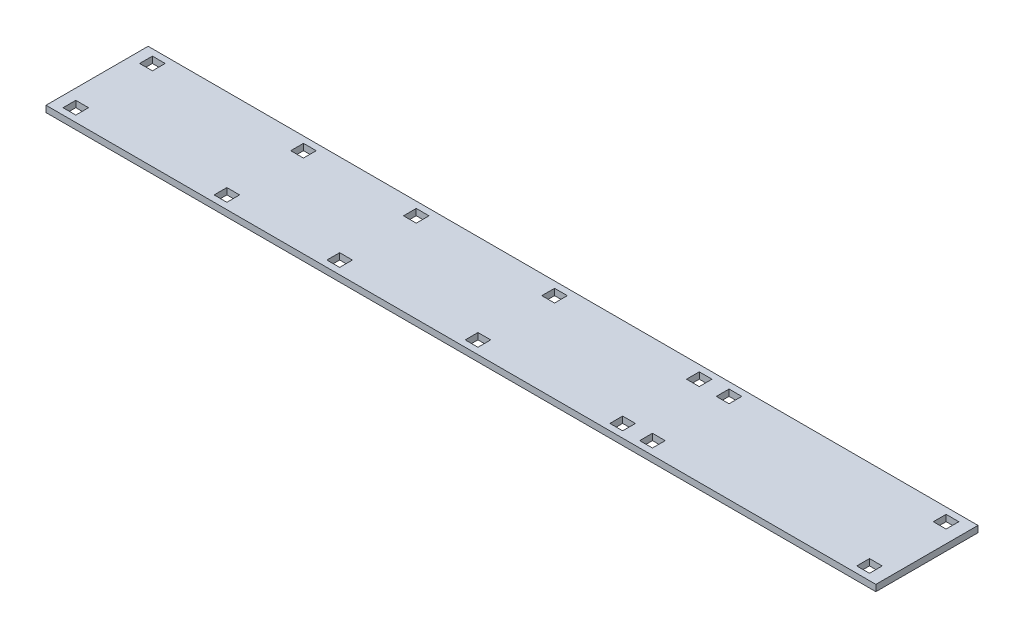
SolidWorks part; units mm, degrees
ref_plane "Front Plane" through (0, 0, 0) normal (0, 0, 1) x (1, 0, 0)
ref_plane "Top Plane" through (0, 0, 0) normal (0, 1, 0) x (1, 0, 0)
ref_plane "Right Plane" through (0, 0, 0) normal (1, 0, 0) x (0, 0, -1)
sketch "Sketch1" plane through (0, 0, 0) normal (0, 1, 0) x (1, 0, 0)
  line L0 (64.5, 4.5) -> (67.5, 4.5)
  line L1 (0, 0) -> (195, 0)
  line L2 (0, 0) -> (0, 24)
  line L3 (0, 24) -> (195, 24)
  line L4 (195, 0) -> (195, 24)
  line L5 (2.5, 22.5) -> (5.5, 22.5)
  line L6 (2.5, 22.5) -> (2.5, 19.5)
  line L7 (2.5, 19.5) -> (5.5, 19.5)
  line L8 (5.5, 22.5) -> (5.5, 19.5)
  line L9 (2.5, 22.5) -> (5.5, 19.5) construction
  line L10 (2.5, 19.5) -> (5.5, 22.5) construction
  line L11 (64.5, 4.5) -> (64.5, 1.5)
  line L12 (64.5, 1.5) -> (67.5, 1.5)
  line L13 (67.5, 4.5) -> (67.5, 1.5)
  line L14 (64.5, 4.5) -> (67.5, 1.5) construction
  line L15 (64.5, 1.5) -> (67.5, 4.5) construction
  line L16 (38, 4.5) -> (41, 4.5)
  line L17 (97, 4.5) -> (100, 4.5)
  line L18 (97, 4.5) -> (97, 1.5)
  line L19 (97, 1.5) -> (100, 1.5)
  line L20 (100, 4.5) -> (100, 1.5)
  line L21 (97, 4.5) -> (100, 1.5) construction
  line L22 (97, 1.5) -> (100, 4.5) construction
  line L23 (38, 4.5) -> (38, 1.5)
  line L24 (38, 1.5) -> (41, 1.5)
  line L25 (41, 4.5) -> (41, 1.5)
  line L26 (38, 4.5) -> (41, 1.5) construction
  line L27 (38, 1.5) -> (41, 4.5) construction
  line L28 (138, 4.5) -> (141, 4.5)
  line L29 (138, 22.5) -> (141, 22.5)
  line L30 (138, 22.5) -> (138, 19.5)
  line L31 (138, 19.5) -> (141, 19.5)
  line L32 (141, 22.5) -> (141, 19.5)
  line L33 (138, 22.5) -> (141, 19.5) construction
  line L34 (138, 19.5) -> (141, 22.5) construction
  line L35 (138, 4.5) -> (138, 1.5)
  line L36 (138, 1.5) -> (141, 1.5)
  line L37 (141, 4.5) -> (141, 1.5)
  line L38 (138, 4.5) -> (141, 1.5) construction
  line L39 (138, 1.5) -> (141, 4.5) construction
  line L40 (131, 4.5) -> (134, 4.5)
  line L41 (131, 22.5) -> (134, 22.5)
  line L42 (131, 22.5) -> (131, 19.5)
  line L43 (131, 19.5) -> (134, 19.5)
  line L44 (134, 22.5) -> (134, 19.5)
  line L45 (131, 22.5) -> (134, 19.5) construction
  line L46 (131, 19.5) -> (134, 22.5) construction
  line L47 (131, 4.5) -> (131, 1.5)
  line L48 (131, 1.5) -> (134, 1.5)
  line L49 (134, 4.5) -> (134, 1.5)
  line L50 (131, 4.5) -> (134, 1.5) construction
  line L51 (131, 1.5) -> (134, 4.5) construction
  line L52 (64.5, 22.5) -> (67.5, 22.5)
  line L53 (97, 22.5) -> (100, 22.5)
  line L54 (97, 22.5) -> (97, 19.5)
  line L55 (97, 19.5) -> (100, 19.5)
  line L56 (100, 22.5) -> (100, 19.5)
  line L57 (97, 22.5) -> (100, 19.5) construction
  line L58 (97, 19.5) -> (100, 22.5) construction
  line L59 (64.5, 22.5) -> (64.5, 19.5)
  line L60 (64.5, 19.5) -> (67.5, 19.5)
  line L61 (67.5, 22.5) -> (67.5, 19.5)
  line L62 (64.5, 22.5) -> (67.5, 19.5) construction
  line L63 (64.5, 19.5) -> (67.5, 22.5) construction
  line L64 (38, 22.5) -> (41, 22.5)
  line L65 (2.5, 4.5) -> (5.5, 4.5)
  line L66 (2.5, 4.5) -> (2.5, 1.5)
  line L67 (2.5, 1.5) -> (5.5, 1.5)
  line L68 (5.5, 4.5) -> (5.5, 1.5)
  line L69 (2.5, 4.5) -> (5.5, 1.5) construction
  line L70 (2.5, 1.5) -> (5.5, 4.5) construction
  line L71 (38, 22.5) -> (38, 19.5)
  line L72 (38, 19.5) -> (41, 19.5)
  line L73 (41, 22.5) -> (41, 19.5)
  line L74 (38, 22.5) -> (41, 19.5) construction
  line L75 (38, 19.5) -> (41, 22.5) construction
  line L76 (189, 22.5) -> (192, 22.5)
  line L77 (189, 4.5) -> (192, 4.5)
  line L78 (189, 4.5) -> (189, 1.5)
  line L79 (189, 1.5) -> (192, 1.5)
  line L80 (192, 4.5) -> (192, 1.5)
  line L81 (189, 4.5) -> (192, 1.5) construction
  line L82 (189, 1.5) -> (192, 4.5) construction
  line L83 (189, 22.5) -> (189, 19.5)
  line L84 (189, 19.5) -> (192, 19.5)
  line L85 (192, 22.5) -> (192, 19.5)
  line L86 (189, 22.5) -> (192, 19.5) construction
  line L87 (189, 19.5) -> (192, 22.5) construction
  point P10 (4, 21)
  point P14 (66, 3)
  point P15 (13.8504, 11.5574)
  point P16 (0, 0)
  point P22 (98.5, 3)
  point P26 (39.5, 3)
  point P32 (139.5, 21)
  point P36 (139.5, 3)
  point P42 (132.5, 21)
  point P46 (132.5, 3)
  point P47 (25.6536, 17.9962)
  point P53 (98.5, 21)
  point P57 (66, 21)
  point P63 (4, 3)
  point P67 (39.5, 21)
  point P73 (190.5, 3)
  point P77 (190.5, 21)
  point P78 (47.2013, 9.4586)
  point P79 (50.0678, 15.2563)
  point P80 (0, 0)
  point P81 (0, 0)
  point P82 (32.4668, 7.9426)
  point P83 (0, 0)
  point P84 (0, 0)
  point P85 (0, 0)
  point P86 (0, 0)
  point P87 (0, 0)
  point P88 (0, 0)
  point P89 (0, 0)
  point P90 (17.6787, 18.4711)
  dimension "D1" = 24
  dimension "D2" = 195
  dimension "D3" = 3
  dimension "D4" = 18
  dimension "D5" = 3
  dimension "D6" = 35.5
  dimension "D7" = 26.5
  dimension "D8" = 32.5
  dimension "D9" = 34
  dimension "D10" = 51
  dimension "D11" = 7
  dimension "D12" = 4
extrude "Boss-Extrude1" add sketch "Sketch1" along normal blind 1.5
